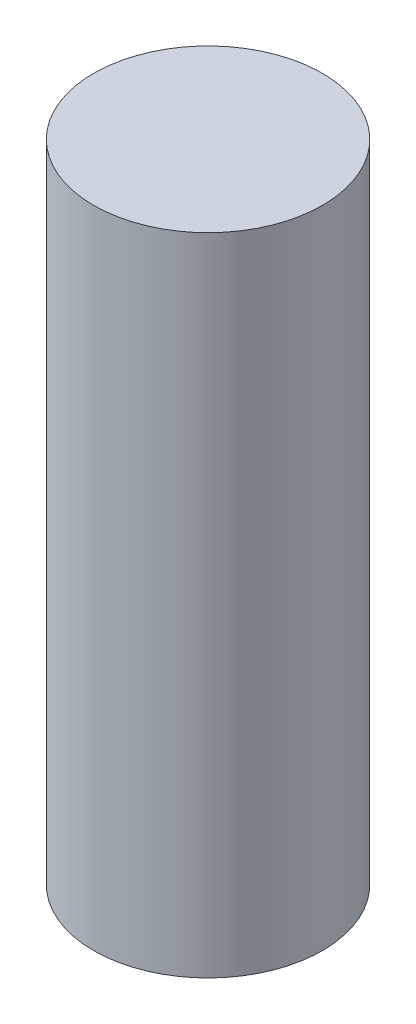
SolidWorks part; units mm, degrees
material "Сталь ШХ15 ГОСТ 801-78"
ref_plane "Plane1" through (0, 0, 0) normal (0, 0, 1) x (1, 0, 0)
ref_plane "Plane2" through (0, 0, 0) normal (0, 1, 0) x (1, 0, 0)
ref_plane "Plane3" through (0, 0, 0) normal (1, 0, 0) x (0, 0, -1)
sketch "Эскиз1" plane through (0, 0, 0) normal (0, 1, 0) x (1, 0, 0)
  circle A0 centre (0, 0) radius 5
  dimension "D1" = 10
extrude "Бобышка-Вытянуть1" add sketch "Эскиз1" along normal up to surface (28.2135 mm away)
